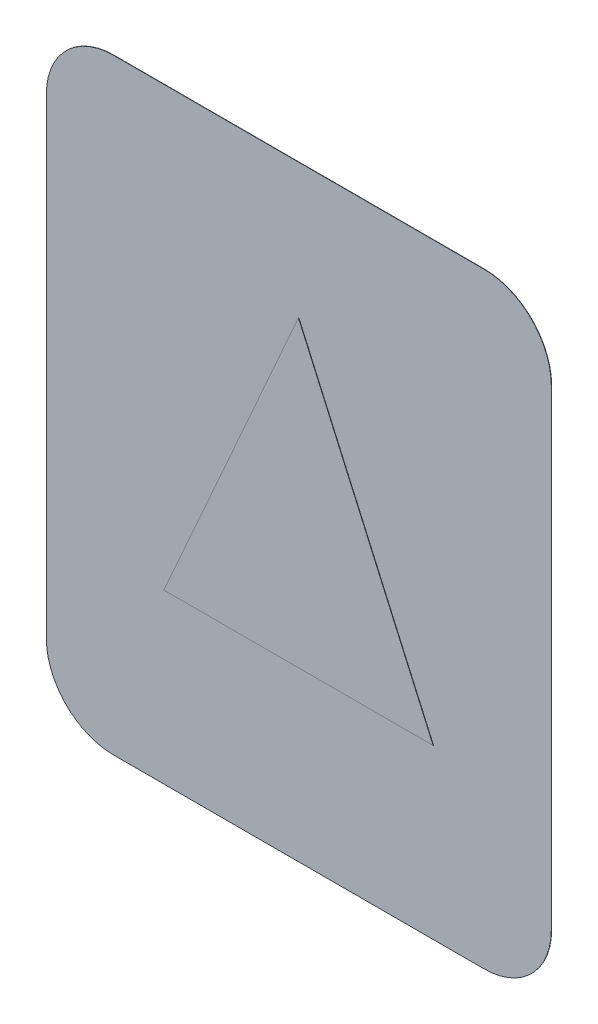
SolidWorks part; units mm, degrees
ref_plane "Alzado" through (0, 0, 0) normal (0, 0, 1) x (1, 0, 0)
ref_plane "Planta" through (0, 0, 0) normal (0, 1, 0) x (1, 0, 0)
ref_plane "Vista lateral" through (0, 0, 0) normal (1, 0, 0) x (0, 0, -1)
sketch "Croquis1" plane through (0, 0, 0) normal (0, 0, 1) x (1, 0, 0)
  line L1 (-47.7083, 74.7396) -> (62.2917, 74.7396)
  line L2 (-67.7083, 54.7396) -> (-67.7083, -85.2604)
  line L3 (-47.7083, -105.2604) -> (62.2917, -105.2604)
  line L4 (82.2917, 54.7396) -> (82.2917, -85.2604)
  arc A0 (-67.7083, 54.7396) -> (-47.7083, 74.7396) centre (-47.7083, 54.7396) cw
  arc A1 (82.2917, 54.7396) -> (62.2917, 74.7396) centre (62.2917, 54.7396) ccw
  arc A2 (62.2917, -105.2604) -> (82.2917, -85.2604) centre (62.2917, -85.2604) ccw
  arc A3 (-67.7083, -85.2604) -> (-47.7083, -105.2604) centre (-47.7083, -85.2604) ccw
  point P6 (-67.7083, 74.7396)
  point P9 (82.2917, 74.7396)
  point P12 (82.2917, -105.2604)
  dimension "D3" = 20
  dimension "D4" = 20
  dimension "D5" = 20
  dimension "D6" = 20
  dimension "D1" = 150
  dimension "D2" = 180
extrude "Saliente-Extruir2" add sketch "Croquis1" along normal blind 0.1 contours L1 A1 L4 A2 L3 A3 L2 A0
sketch "Croquis2" plane through (0, 0, 0.1) normal (0, 0, 1) x (1, 0, 0)
  line L0 (-32.7083, -55.2604) -> (7.2917, 34.7396)
  line L1 (7.2917, 34.7396) -> (47.2917, -55.2604)
  line L2 (47.2917, -55.2604) -> (-32.7083, -55.2604)
  line L3 (-47.7083, -105.2604) -> (62.2917, -105.2604) construction
  line L4 (82.2917, 54.7396) -> (82.2917, -85.2604) construction
  dimension "D1" = 75
  dimension "D2" = 50
  dimension "D3" = 80
  dimension "D4" = 35
  dimension "D5" = 90
extrude "Saliente-Extruir3" add sketch "Croquis2" along normal blind 0.1
